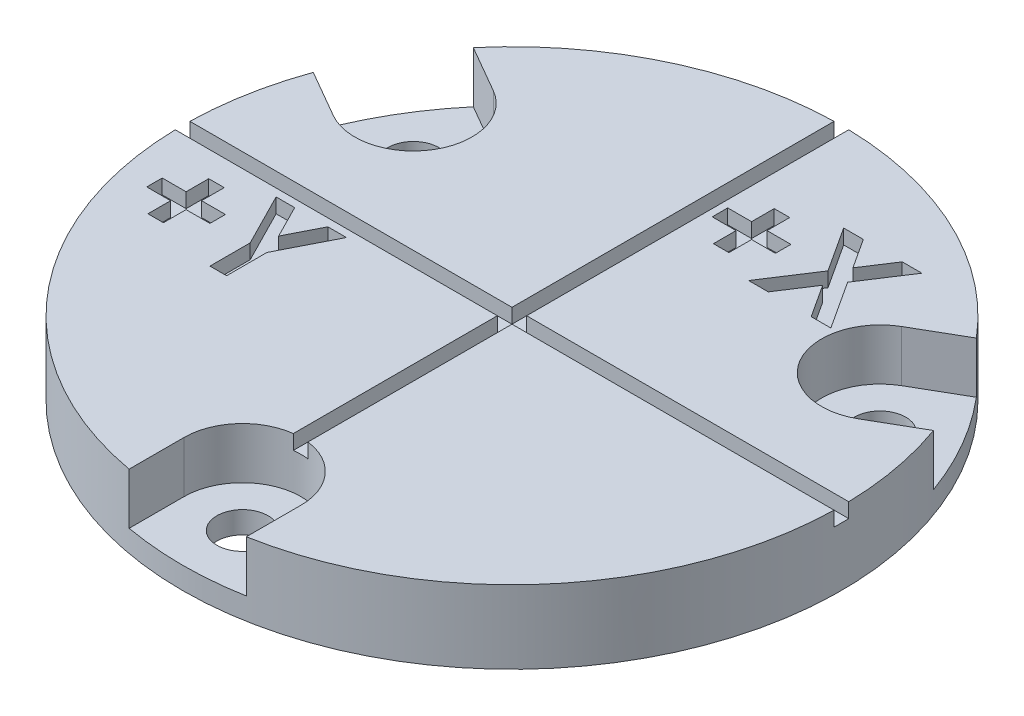
SolidWorks part; units mm, degrees
ref_plane "Front" through (0, 0, 0) normal (0, 0, 1) x (1, 0, 0)
ref_plane "Top" through (0, 0, 0) normal (0, 1, 0) x (1, 0, 0)
ref_plane "Right" through (0, 0, 0) normal (1, 0, 0) x (0, 0, -1)
sketch "Sketch1" plane through (0, 0, 0) normal (0, 1, 0) x (1, 0, 0)
  line L0 (0, 22.5) -> (0, -22.5) construction
  line L1 (22.5, 0) -> (-22.5, 0) construction
  circle A0 centre (0, 0) radius 22.5
  circle A1 centre (0, 0) radius 18.4 construction
  point P19 (0, 0)
  dimension "D1" = 45
  dimension "D2" = 36.8
extrude "plate" add sketch "Sketch1" along normal blind 5
sketch "Sketch6" plane through (0, 5, 0) normal (0, 1, 0) x (1, 0, 0)
  line L0 (0, 22.5) -> (0, -22.5) construction
  line L1 (0, -22.5) -> (0, -18.4) construction
  line L2 (-4, -22.5) -> (-4, -18.4)
  line L3 (4, -22.5) -> (4, -18.4)
  circle A1 centre (0, 0) radius 18.4 construction
  circle A2 centre (0, 0) radius 22.5 construction
  arc A3 (-4, -22.5) -> (4, -22.5) centre (0, -22.5) ccw
  arc A4 (4, -18.4) -> (-4, -18.4) centre (0, -18.4) ccw
  point P7 (0, -20.45)
  dimension "D1" = 4
extrude "opening for screw" cut sketch "Sketch6" against normal blind 5 from offset 1.5 contours L3 A4 L2 A3
sketch "Sketch7" plane through (0, 1.5, 0) normal (0, 1, 0) x (1, 0, 0)
  line L0 (0, 22.5) -> (0, -22.5) construction
  circle A0 centre (0, -18.4) radius 1.75
  circle A1 centre (0, 0) radius 18.4 construction
  point P2 (0, 0)
  dimension "D1" = 3.5
extrude "screw hole" cut sketch "Sketch7" against normal blind 5
pattern_circular "CirPattern20" count 3 over 360 about axis through (0, 0, 0) along (0, 1, 0) of "opening for screw", "screw hole"
sketch "Sketch10" plane through (0, 5, 0) normal (0, 1, 0) x (1, 0, 0)
  line L1 (-22.5, 0.5) -> (22.5, 0.5)
  line L2 (-22.5, 0.5) -> (-22.5, -0.5)
  line L3 (-22.5, -0.5) -> (22.5, -0.5)
  line L4 (22.5, 0.5) -> (22.5, -0.5)
  line L5 (-0.5, 22.5) -> (0.5, 22.5)
  line L6 (-0.5, 22.5) -> (-0.5, -22.5)
  line L7 (-0.5, -22.5) -> (0.5, -22.5)
  line L8 (0.5, 22.5) -> (0.5, -22.5)
  line L9 (0, 22.5) -> (0, -22.5) construction
  point P4 (22.5, 0)
  point P9 (-22.5, 0)
  point P14 (0, -22.5)
  point P15 (0, 22.5)
  point P19 (-2.0585, 12.7822)
  point P20 (-4.7401, 12.405)
  point P22 (-18.9752, -6.3427)
  point P23 (0, 0)
  point P24 (-18.8339, -7.6497)
  point P25 (1.0987, 13.1019)
  point P26 (1.3556, 11.6943)
  point P27 (0, 0)
  point P28 (0.5, 11.933)
  dimension "D1" = 1
  dimension "D2" = 1
extrude "Cut-Extrude5" cut sketch "Sketch10" against normal blind 1 contours L6 L7 L8 L5 | L1 L4 L3 L2
sketch "Sketch11" plane through (0, 5, 0) normal (0, 1, 0) x (1, 0, 0)
  line L0 (0.5, 22.4944) -> (0.5, 0.5) construction
  text T0 "<b>+X</b>"
  text T1 "<b>+Y</b>"
  point P1 (1.2612, 8.3302)
  point P2 (0, 0)
  point P3 (0, 0)
  point P4 (0.5, 10.1604)
  point P8 (0, 0)
  point P9 (-17.4006, -2.4788)
  point P10 (-19.5952, -5.1924)
  point P11 (-20.5748, -7.3769)
extrude "Cut-Extrude6" cut sketch "Sketch11" against normal blind 1
